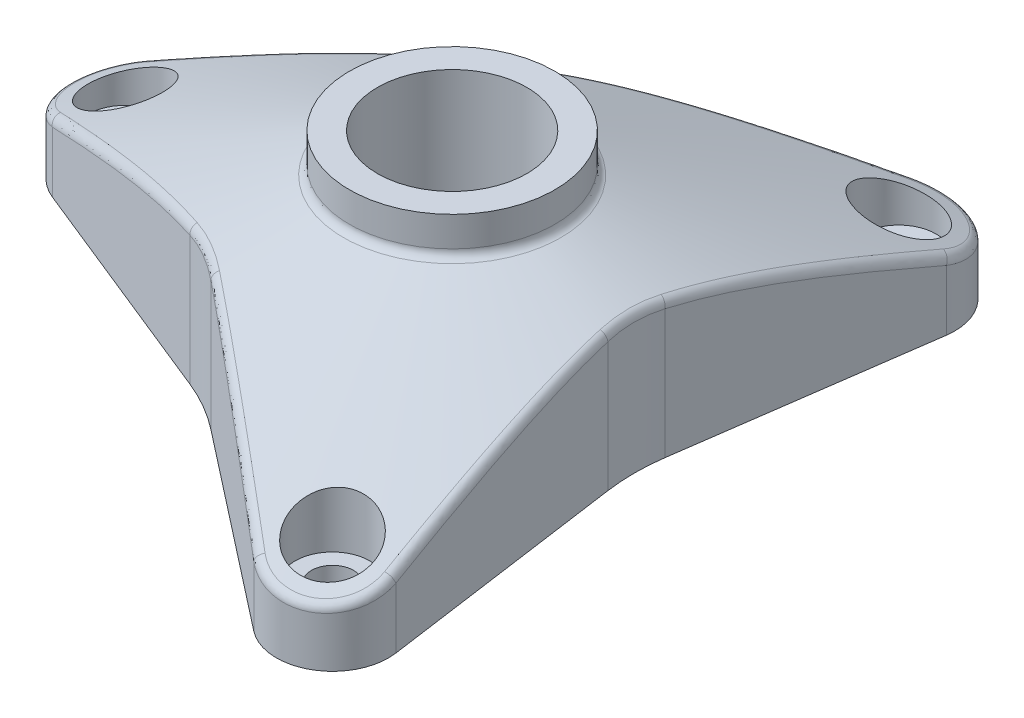
SolidWorks part; units mm, degrees
material "Plain Carbon Steel"
ref_plane "Front Plane" through (0, 0, 0) normal (0, 0, 1) x (1, 0, 0)
ref_plane "Top Plane" through (0, 0, 0) normal (0, 1, 0) x (1, 0, 0)
ref_plane "Right Plane" through (0, 0, 0) normal (1, 0, 0) x (0, 0, -1)
sketch "Sketch1" plane through (0, 0, 0) normal (0, 1, 0) x (1, 0, 0)
  line L0 (0, 0) -> (28.6655, 49.6501) construction
  line L1 (0, 0) -> (-85.3158, 0) construction
  line L2 (0, 0) -> (38.3382, -66.4037) construction
  line L3 (-37.2476, -5.5631) -> (-12.5163, -15.5552)
  line L4 (-37.2476, 5.5631) -> (-12.5163, 15.5552)
  line L5 (23.4416, 29.4759) -> (19.7294, 3.0618)
  line L6 (13.806, 35.039) -> (-7.2131, 18.617)
  line L7 (13.806, -35.039) -> (-7.2131, -18.617)
  line L8 (23.4416, -29.4759) -> (19.7294, -3.0618)
  circle A0 centre (0, 0) radius 35 construction
  arc A2 (-37.2476, 5.5631) -> (-37.2476, -5.5631) centre (-35, 0) ccw
  circle A3 centre (0, 0) radius 35 construction
  arc A6 (13.806, -35.039) -> (23.4416, -29.4759) centre (17.5, -30.3109) ccw
  arc A7 (19.7294, -3.0618) -> (19.7294, 3.0618) centre (41.5153, 0) cw
  arc A8 (-7.2131, 18.617) -> (-12.5163, 15.5552) centre (-20.7576, 35.9533) cw
  arc A9 (-7.2131, -18.617) -> (-12.5163, -15.5552) centre (-20.7576, -35.9533) ccw
  arc A10 (23.4416, 29.4759) -> (13.806, 35.039) centre (17.5, 30.3109) ccw
  point P14 (-9.6495, -16.7135)
  point P18 (0, 0)
  point P20 (0, 0)
  point P28 (0, 0)
  dimension "D3" = 70
  dimension "D4" = 22
  dimension "D5" = 12
  dimension "D1" = 120
  dimension "D2" = 120
  dimension "D6" = 22
  dimension "D7" = 22
extrude "Boss-Extrude1" add sketch "Sketch1" along normal blind 22
sketch "Sketch2" plane through (0, 0, 0) normal (0, 0, 1) x (1, 0, 0)
  line L0 (0, 0) -> (0, 48.2821) construction
  line L1 (0, 22) -> (-11, 22)
  line L2 (13.806, 22) -> (-7.2131, 22) construction
  line L3 (-12.5163, 22) -> (-37.2476, 22) construction
  line L4 (-11, 22) -> (-11, 18.1208)
  line L5 (-11, 18.1208) -> (-41, 6)
  line L6 (-41, 0) -> (-37.2476, 0) construction
  line L7 (0, 22) -> (0, 30.6731)
  line L8 (0, 30.6731) -> (-46.0665, 30.6731)
  line L9 (-46.0665, 30.6731) -> (-41, 6)
  line L10 (-41, 22) -> (-41, 0) construction
  point P11 (-11, 18.1208)
  point P15 (-40.5729, 6)
  dimension "D1" = 11
  dimension "D2" = 6
  dimension "D3" = 112
revolve "Cut-Revolve1" cut sketch "Sketch2" angle 360 about L0
sketch "Sketch3" plane through (0, 22, 0) normal (0, 1, 0) x (1, 0, 0)
  circle A0 centre (0, 0) radius 8
  dimension "D1" = 16
extrude "Cut-Extrude1" cut sketch "Sketch3" against normal blind 30
sketch "Sketch4" plane through (0, 0, 0) normal (0, -1, 0) x (1, 0, 0)
  circle A0 centre (17.5, 30.3109) radius 2.25
  dimension "D1" = 4.5
extrude "Cut-Extrude2" cut sketch "Sketch4" against normal blind 4
sketch "Sketch5" plane through (0, 4, 0) normal (0, -1, 0) x (1, 0, 0)
  circle A0 centre (17.5, 30.3109) radius 4
  dimension "D1" = 8
extrude "Cut-Extrude3" cut sketch "Sketch5" against normal blind 7
pattern_circular "CirPattern1" count 3 over 360 about axis through (0, 0, 0) along (0, 1, 0) of "Cut-Extrude3", "Cut-Extrude2"
fillet "Fillet1" radius 1 13 edges at (21.3151, 6.0283, 34.9418) (-7.9246, 14.588, 18.0839) (-40.918, 6.0283, 0.9885) (-11.6988, 14.588, -15.9049) (19.6029, 6.0283, -35.9303) (19.6234, 14.588, -2.1791) (0, 18.1208, -11)
